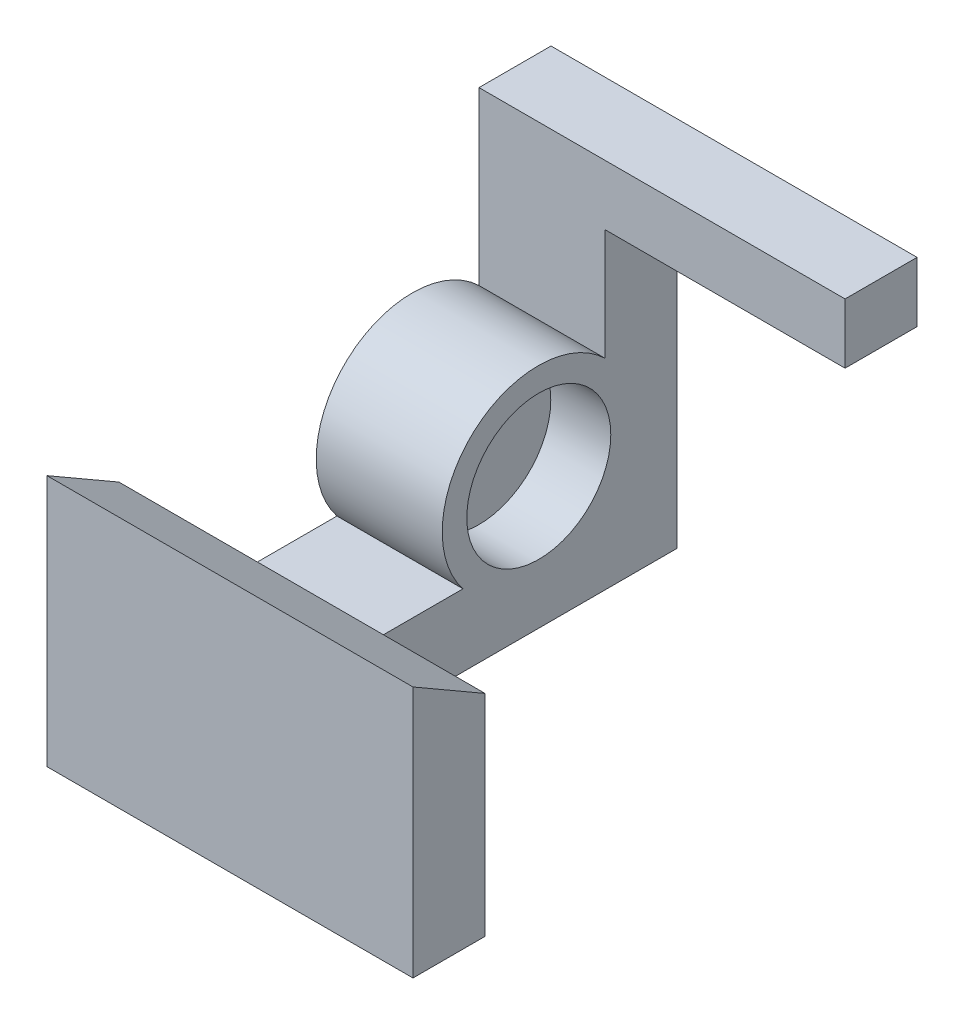
SolidWorks part; units mm, degrees
ref_plane "Front Plane" through (0, 0, 0) normal (0, 0, 1) x (1, 0, 0)
ref_plane "Top Plane" through (0, 0, 0) normal (0, 1, 0) x (1, 0, 0)
ref_plane "Right Plane" through (0, 0, 0) normal (1, 0, 0) x (0, 0, -1)
sketch "Sketch2" plane through (0, 0, 0) normal (1, 0, 0) x (0, 0, -1)
  line L1 (2.7118, 20.9603) -> (-3.2882, 20.9603)
  line L2 (2.7118, 20.9603) -> (2.7118, -5.0397)
  line L4 (-3.2882, 20.9603) -> (-3.2882, 11.6764)
  line L5 (-15.1224, 0.9603) -> (-33.2882, 0.9603)
  line L7 (2.7118, -5.0397) -> (-33.2882, -5.0397)
  line L8 (-33.2882, 0.9603) -> (-33.2882, -5.0397)
  arc A0 (-3.2882, 11.6764) -> (-15.1224, 0.9603) centre (-8.8511, 5.9272) ccw
  dimension "D4" = 30
  dimension "D5" = 16
  dimension "D1" = 6
  dimension "D2" = 6
  dimension "D3" = 20
extrude "Boss-Extrude1" add sketch "Sketch2" against normal blind 10.5
sketch "Sketch4" plane through (0, 20.9603, 0) normal (0, 1, 0) x (1, 0, 0)
  line L1 (-10.5, 2.7118) -> (20, 2.7118)
  line L2 (-10.5, 2.7118) -> (-10.5, -3.2882)
  line L3 (-10.5, -3.2882) -> (20, -3.2882)
  line L4 (20, 2.7118) -> (20, -3.2882)
  dimension "D1" = 20
extrude "Boss-Extrude2" add sketch "Sketch4" along normal blind 5
sketch "Sketch5" plane through (0, 0, 33.2882) normal (0, 0, 1) x (1, 0, 0)
  line L1 (-10.5, -5.0397) -> (20, -5.0397)
  line L2 (-10.5, -5.0397) -> (-10.5, 0.9603)
  line L3 (-10.5, 0.9603) -> (20, 0.9603)
  line L4 (20, -5.0397) -> (20, 0.9603)
  dimension "D1" = 20
extrude "Boss-Extrude3" add sketch "Sketch5" along normal blind 6
sketch "Sketch6" plane through (0, 0, 0) normal (1, 0, 0) x (0, 0, -1)
  circle A0 centre (-8.8069, 5.9239) radius 6
extrude "Cut-Extrude2" cut sketch "Sketch6" against normal blind 5
sketch "Sketch11" plane through (0, 0.9603, 0) normal (0, 1, 0) x (1, 0, 0)
  line L0 (-10.5, -15.1224) -> (-10.5, -39.2882) construction
  line L1 (20, -39.2882) -> (-10.5, -39.2882)
  line L2 (20, -39.2882) -> (20, -33.2882)
  line L3 (20, -33.2882) -> (-10.5, -33.2882)
  line L4 (-10.5, -39.2882) -> (-10.5, -33.2882)
extrude "Boss-Extrude5" add sketch "Sketch11" along normal blind 15
sketch "Sketch12" plane through (-10.5, 0, 0) normal (-1, 0, 0) x (0, 0, 1)
  line L0 (33.2882, 15.9603) -> (39.2882, 15.9603)
  line L1 (39.2882, 15.9603) -> (33.2882, 12.4962)
  line L2 (33.2882, 15.9603) -> (33.2882, 0.9603) construction
  line L3 (33.2882, 12.4962) -> (33.2882, 15.9603)
  dimension "D1" = 60
extrude "Cut-Extrude4" cut sketch "Sketch12" against normal through all contours L0 L1 L3
